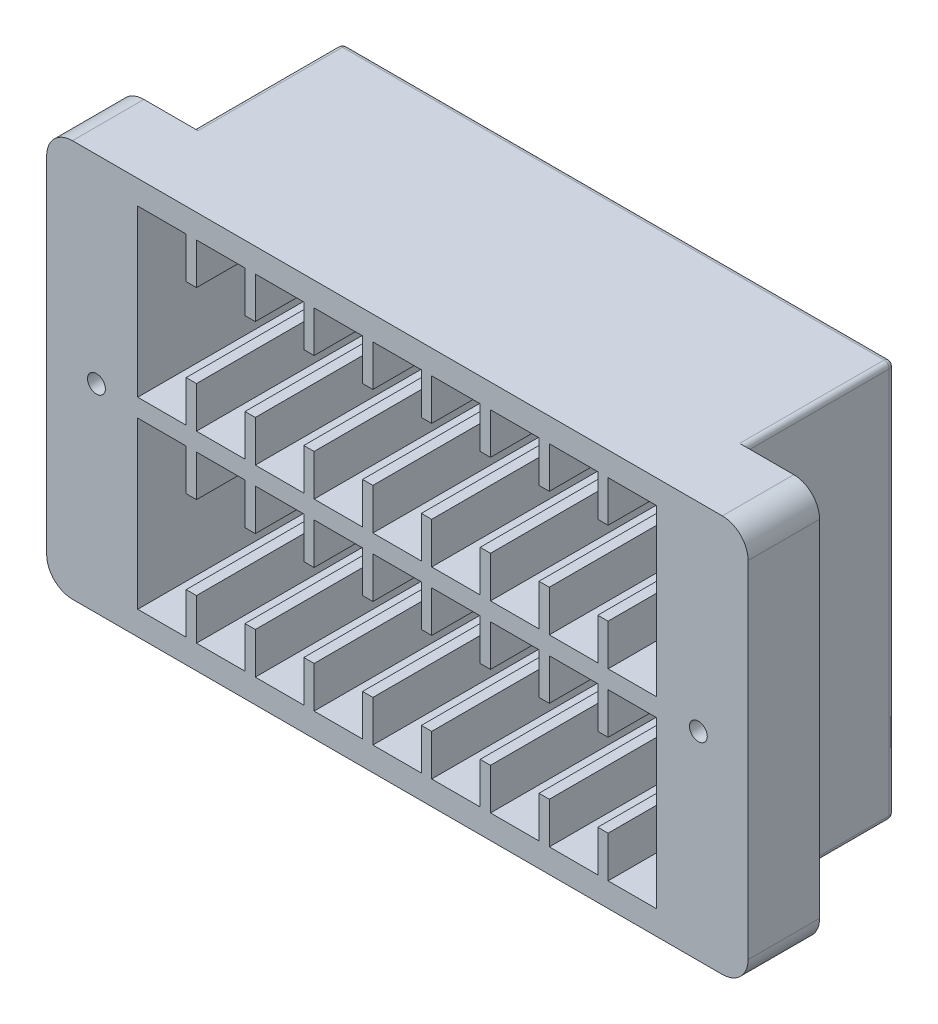
SolidWorks part; units mm, degrees
other "Markup1"
sketch "Sketch6" plane through (68, 38.5, 7.85) normal (0.1509, 0.4092, 0.8999) x (-0.9102, 0.4126, -0.035)
ref_plane "Front Plane" through (0, 0, 0) normal (0, 0, 1) x (1, 0, 0)
ref_plane "Top Plane" through (0, 0, 0) normal (0, 1, 0) x (1, 0, 0)
ref_plane "Right Plane" through (0, 0, 0) normal (1, 0, 0) x (0, 0, -1)
sketch "Sketch1" plane through (0, 0, 0) normal (0, 0, 1) x (1, 0, 0)
  line L0 (58.35, 0) -> (-58.35, 0) construction
  line L1 (68, -38.5) -> (-68, -38.5)
  line L2 (68, -38.5) -> (68, 38.5)
  line L3 (68, 38.5) -> (-68, 38.5)
  line L4 (-68, -38.5) -> (-68, 38.5)
  line L5 (68, -38.5) -> (-68, 38.5) construction
  line L6 (68, 38.5) -> (-68, -38.5) construction
  line L7 (-58.35, -1.725) -> (-58.35, 1.725) construction
  circle A0 centre (-58.35, 0) radius 1.725
  circle A1 centre (58.35, 0) radius 1.725
  point P0 (0, 0)
  point P9 (0, 0)
  point P11 (-58.35, -21.85)
  point P16 (-58.35, 21.85)
  point P24 (-58.35, 0)
  dimension "D4" = 3.45
  dimension "D1" = 136
  dimension "D2" = 77
  dimension "D3" = 116.7
extrude "Boss-Extrude1" add sketch "Sketch1" along normal blind 7.85 and the other way blind 6
sketch "Sketch2" plane through (0, 0, -6) normal (0, 0, -1) x (-1, 0, 0)
  line L0 (-68, 38.5) -> (68, 38.5) construction
  line L1 (53.5, -38.5) -> (-53.5, -38.5)
  line L2 (53.5, -38.5) -> (53.5, 38.5)
  line L3 (53.5, 38.5) -> (-53.5, 38.5)
  line L4 (-53.5, -38.5) -> (-53.5, 38.5)
  line L5 (53.5, -38.5) -> (-53.5, 38.5) construction
  line L6 (53.5, 38.5) -> (-53.5, -38.5) construction
  point P0 (0, 0)
  dimension "D1" = 107
extrude "Boss-Extrude2" add sketch "Sketch2" along normal blind 29
sketch "Sketch3" plane through (0, 0, 7.85) normal (0, 0, 1) x (1, 0, 0)
  line L0 (0, -1.75) -> (0, 1.75) construction
  line L6 (48.4799, 33.85) -> (40.85, 33.85)
  line L19 (50.35, 0) -> (-50.35, 0) construction
  line L20 (-38.95, 33.85) -> (-38.95, 25.85)
  line L21 (-50.35, 33.85) -> (-40.95, 33.85)
  line L22 (-50.35, 33.85) -> (-50.35, 1.75)
  line L24 (-40.95, 33.85) -> (-40.95, 25.85)
  line L25 (-38.95, 33.85) -> (-29.55, 33.85)
  line L26 (-29.55, 33.85) -> (-29.55, 25.85)
  line L40 (-27.55, 33.85) -> (-27.55, 25.85)
  line L41 (-27.55, 33.85) -> (-18.15, 33.85)
  line L75 (-18.15, 33.85) -> (-18.15, 25.85)
  line L77 (-16.15, 33.85) -> (-16.15, 25.85)
  line L93 (-16.15, 33.85) -> (-6.75, 33.85)
  line L94 (-6.75, 33.85) -> (-6.75, 25.85)
  line L96 (-4.75, 33.85) -> (-4.75, 25.85)
  line L98 (-4.75, 33.85) -> (4.65, 33.85)
  line L99 (4.65, 33.85) -> (4.65, 25.85)
  line L101 (6.65, 33.85) -> (6.65, 25.85)
  line L102 (6.65, 33.85) -> (16.05, 33.85)
  line L103 (16.05, 33.85) -> (16.05, 25.85)
  line L105 (18.05, 33.85) -> (18.05, 25.85)
  line L106 (18.05, 33.85) -> (27.45, 33.85)
  line L107 (27.45, 33.85) -> (27.45, 25.85)
  line L109 (29.45, 33.85) -> (29.45, 25.85)
  line L110 (29.45, 33.85) -> (38.85, 33.85)
  line L111 (38.85, 33.85) -> (38.85, 25.85)
  line L113 (40.85, 33.85) -> (40.85, 25.85)
  line L114 (40.85, 33.85) -> (50.25, 33.85)
  line L115 (50.25, 33.85) -> (50.25, 1.75)
  line L118 (2.9667, -1.75) -> (-5.3771, 1.75) construction
  line L119 (3.1755, 1.75) -> (-3.1755, -1.75) construction
  line L155 (-40.95, 25.85) -> (-38.95, 25.85)
  line L165 (-50.35, 1.75) -> (-50.35, 33.85)
  line L166 (-29.55, 25.85) -> (-27.55, 25.85)
  line L167 (-18.15, 25.85) -> (-16.15, 25.85)
  line L168 (-6.75, 25.85) -> (-4.75, 25.85)
  line L169 (4.65, 25.85) -> (6.65, 25.85)
  line L170 (16.05, 25.85) -> (18.05, 25.85)
  line L171 (27.45, 25.85) -> (29.45, 25.85)
  line L173 (38.85, 25.85) -> (40.85, 25.85)
  line L174 (-50.35, 1.75) -> (50.25, 1.75)
  line L175 (-50.35, -1.75) -> (50.25, -1.75)
  line L176 (-40.95, 33.85) -> (-50.35, 33.85)
  line L177 (-29.55, 33.85) -> (-38.95, 33.85)
  line L178 (-18.15, 33.85) -> (-27.55, 33.85)
  line L179 (-6.75, 33.85) -> (-16.15, 33.85)
  line L180 (4.65, 33.85) -> (-4.75, 33.85)
  line L181 (16.05, 33.85) -> (6.65, 33.85)
  line L182 (27.45, 33.85) -> (18.05, 33.85)
  line L183 (38.85, 33.85) -> (29.45, 33.85)
  point P0 (0, 0)
  point P2 (0, 0)
  point P10 (0, 0)
  point P11 (0, 0)
  point P14 (0, 0)
  point P42 (0, 0)
  point P45 (0, 0)
  dimension "D2" = 32.1
  dimension "D3" = 9.4
  dimension "D4" = 2
  dimension "D5" = 9
  dimension "D7" = 8
  dimension "D6" = 50.35
  dimension "D15" = 3.5
  dimension "D18" = 100.7
extrude "Cut-Extrude1" cut sketch "Sketch3" against normal blind 32.5 contours L22 L174 L115 L6 L113 L173 L111 L110 L109 L171 L107 L106 L105 L170 L103 L102 L101 L169 L99 L98 L96 L168 L94 L93 L77 L167 L75 L41 L40 L166 L26 L25 L20 L155 L24 L21
mirror "Mirror1" about plane through (0, 0, 0) normal (0, 1, 0) of "Cut-Extrude1"
sketch "Sketch4" plane through (0, 0, 7.85) normal (0, 0, 1) x (1, 0, 0)
  line L0 (-50.35, 1.75) -> (50.25, 1.75) construction
  line L1 (-40.95, 1.75) -> (-38.95, 1.75)
  line L2 (-40.95, 1.75) -> (-40.95, 9.75)
  line L3 (-40.95, 9.75) -> (-38.95, 9.75)
  line L4 (-38.95, 1.75) -> (-38.95, 9.75)
  line L5 (-40.95, 33.85) -> (-40.95, 25.85) construction
  line L6 (-29.55, 1.75) -> (-29.55, 9.75)
  line L7 (-29.55, 1.75) -> (-27.55, 1.75)
  line L8 (-27.55, 1.75) -> (-27.55, 9.75)
  line L9 (-29.55, 9.75) -> (-27.55, 9.75)
  line L10 (-18.15, 1.75) -> (-18.15, 9.75)
  line L11 (-18.15, 1.75) -> (-16.15, 1.75)
  line L12 (-16.15, 1.75) -> (-16.15, 9.75)
  line L13 (-18.15, 9.75) -> (-16.15, 9.75)
  line L14 (-6.75, 1.75) -> (-6.75, 9.75)
  line L15 (-6.75, 1.75) -> (-4.75, 1.75)
  line L16 (-4.75, 1.75) -> (-4.75, 9.75)
  line L17 (-6.75, 9.75) -> (-4.75, 9.75)
  line L18 (4.65, 1.75) -> (4.65, 9.75)
  line L19 (4.65, 1.75) -> (6.65, 1.75)
  line L20 (6.65, 1.75) -> (6.65, 9.75)
  line L21 (4.65, 9.75) -> (6.65, 9.75)
  line L22 (16.05, 1.75) -> (16.05, 9.75)
  line L23 (16.05, 1.75) -> (18.05, 1.75)
  line L24 (18.05, 1.75) -> (18.05, 9.75)
  line L25 (16.05, 9.75) -> (18.05, 9.75)
  line L26 (27.45, 1.75) -> (27.45, 9.75)
  line L27 (27.45, 1.75) -> (29.45, 1.75)
  line L28 (29.45, 1.75) -> (29.45, 9.75)
  line L29 (27.45, 9.75) -> (29.45, 9.75)
  line L30 (38.85, 1.75) -> (38.85, 9.75)
  line L31 (38.85, 1.75) -> (40.85, 1.75)
  line L32 (40.85, 1.75) -> (40.85, 9.75)
  line L33 (38.85, 9.75) -> (40.85, 9.75)
  dimension "D1" = 2
  dimension "D2" = 8
  dimension "D4" = 9.4
  dimension "D3" = 8
extrude "Boss-Extrude3" add sketch "Sketch4" against normal up to surface (32.5 mm away) up to face at (-0.05, 28.5111, -24.65)
mirror "Mirror2" about plane through (0, 0, 0) normal (0, 1, 0) of "Boss-Extrude3"
sketch "Sketch5" plane through (0, 0, 7.85) normal (0, 0, 1) x (1, 0, 0)
  line L0 (-40.95, -9.75) -> (-40.95, -1.75) construction
  line L1 (-50.35, -1.75) -> (-40.95, -1.75)
  line L2 (-50.35, -1.75) -> (-50.35, -1.25)
  line L3 (-50.35, -1.25) -> (-40.95, -1.25)
  line L4 (-40.95, -1.75) -> (-40.95, -1.25)
  line L5 (-38.95, -1.75) -> (-38.95, -1.25)
  line L6 (-38.95, -1.75) -> (-29.55, -1.75)
  line L7 (-29.55, -1.75) -> (-29.55, -1.25)
  line L8 (-38.95, -1.25) -> (-29.55, -1.25)
  line L9 (-27.55, -1.75) -> (-27.55, -1.25)
  line L10 (-27.55, -1.75) -> (-18.15, -1.75)
  line L11 (-18.15, -1.75) -> (-18.15, -1.25)
  line L12 (-27.55, -1.25) -> (-18.15, -1.25)
  line L13 (-16.15, -1.75) -> (-16.15, -1.25)
  line L14 (-16.15, -1.75) -> (-6.75, -1.75)
  line L15 (-6.75, -1.75) -> (-6.75, -1.25)
  line L16 (-16.15, -1.25) -> (-6.75, -1.25)
  line L17 (-4.75, -1.75) -> (-4.75, -1.25)
  line L18 (-4.75, -1.75) -> (4.65, -1.75)
  line L19 (4.65, -1.75) -> (4.65, -1.25)
  line L20 (-4.75, -1.25) -> (4.65, -1.25)
  line L21 (6.65, -1.75) -> (6.65, -1.25)
  line L22 (6.65, -1.75) -> (16.05, -1.75)
  line L23 (16.05, -1.75) -> (16.05, -1.25)
  line L24 (6.65, -1.25) -> (16.05, -1.25)
  line L25 (18.05, -1.75) -> (18.05, -1.25)
  line L26 (18.05, -1.75) -> (27.45, -1.75)
  line L27 (27.45, -1.75) -> (27.45, -1.25)
  line L28 (18.05, -1.25) -> (27.45, -1.25)
  line L29 (29.45, -1.75) -> (29.45, -1.25)
  line L30 (29.45, -1.75) -> (38.85, -1.75)
  line L31 (38.85, -1.75) -> (38.85, -1.25)
  line L32 (29.45, -1.25) -> (38.85, -1.25)
  line L33 (40.85, -1.75) -> (40.85, -1.25)
  line L34 (40.85, -1.75) -> (50.25, -1.75)
  line L35 (50.25, -1.75) -> (50.25, -1.25)
  line L36 (40.85, -1.25) -> (50.25, -1.25)
  dimension "D1" = 0.5
  dimension "D3" = 2
  dimension "D2" = 9
extrude "Cut-Extrude2" [suppressed] cut sketch "Sketch5" against normal up to surface (32.5 mm away)
fillet "Fillet1" radius 5 4 edges at (-68, 38.5, 0.925) (68, 38.5, 0.925) (68, -38.5, 0.925) (-68, -38.5, 0.925)
fillet "Fillet3" [suppressed] radius 1
fillet "Fillet4" radius 1 8 edges at (0, 38.5, -35) (-53.5, 0, -35) (0, -38.5, -35) (53.5, 0, -35) (53.5, -38.5, -20.5) (53.5, 38.5, -20.5) (-53.5, 38.5, -20.5) (-53.5, -38.5, -20.5)
